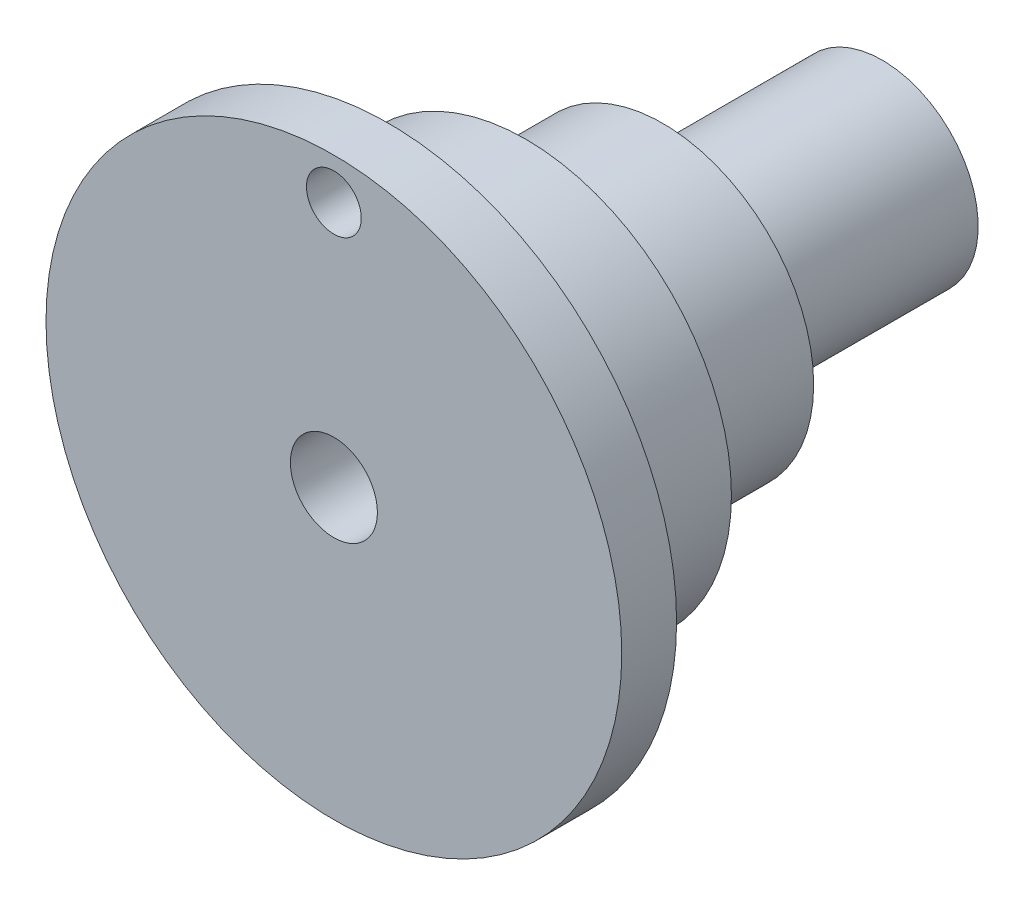
SolidWorks part; units mm, degrees
ref_plane "Front Plane" through (0, 0, 0) normal (0, 0, 1) x (1, 0, 0)
ref_plane "Top Plane" through (0, 0, 0) normal (0, 1, 0) x (1, 0, 0)
ref_plane "Right Plane" through (0, 0, 0) normal (1, 0, 0) x (0, 0, -1)
sketch "Sketch1" plane through (0, 0, 0) normal (0, 0, 1) x (1, 0, 0)
  circle A0 centre (0, 0) radius 1.5875
  circle A1 centre (0, 0) radius 7.5
  dimension "D1" = 3.175
  dimension "D2" = 15
extrude "Boss-Extrude1" add sketch "Sketch1" along normal blind 20 contours A1 | A0
sketch "Sketch2" plane through (0, 0, 20) normal (0, 0, 1) x (1, 0, 0)
  circle A0 centre (0, 0) radius 7.5
  circle A1 centre (0, 0) radius 1.5875
  circle A2 centre (0, 0) radius 10.5
  circle A3 centre (0, 0) radius 7.5 construction
  circle M1 centre (0, 0) radius 7.5
  circle M2 centre (0, 0) radius 1.5875
  dimension "D1" = 3
extrude "Boss-Extrude2" add sketch "Sketch2" against normal blind 2 contours A2 M1 | M1 M2
sketch "Sketch3" plane through (0, 0, 18) normal (0, 0, -1) x (-1, 0, 0)
  line L0 (0, 10.5) -> (0, 7.5) construction
  circle A0 centre (0, 0) radius 10.5 construction
  circle A1 centre (0, 0) radius 7.5 construction
  circle A3 centre (0, 9) radius 1
  dimension "D1" = 2
extrude "Cut-Extrude1" cut sketch "Sketch3" against normal through all
sketch "Sketch4" plane through (0, 0, 0) normal (0, 0, -1) x (-1, 0, 0)
  circle A0 centre (0, 0) radius 7.5
  circle A1 centre (0, 0) radius 5.5
  dimension "D1" = 2
  dimension "D2" = 15
extrude "Cut-Extrude2" cut sketch "Sketch4" against normal offset from surface (13 mm away) 5 up to face at (-1, 9, 18)
sketch "Sketch5" plane through (0, 0, 0) normal (0, 0, -1) x (-1, 0, 0)
  circle A0 centre (0, 0) radius 5.5
  circle A1 centre (0, 0) radius 3.5
  dimension "D1" = 2
  dimension "D2" = 11
extrude "Cut-Extrude3" cut sketch "Sketch5" against normal offset from surface (8 mm away) 5 up to face at (7.5, 0, 13)
